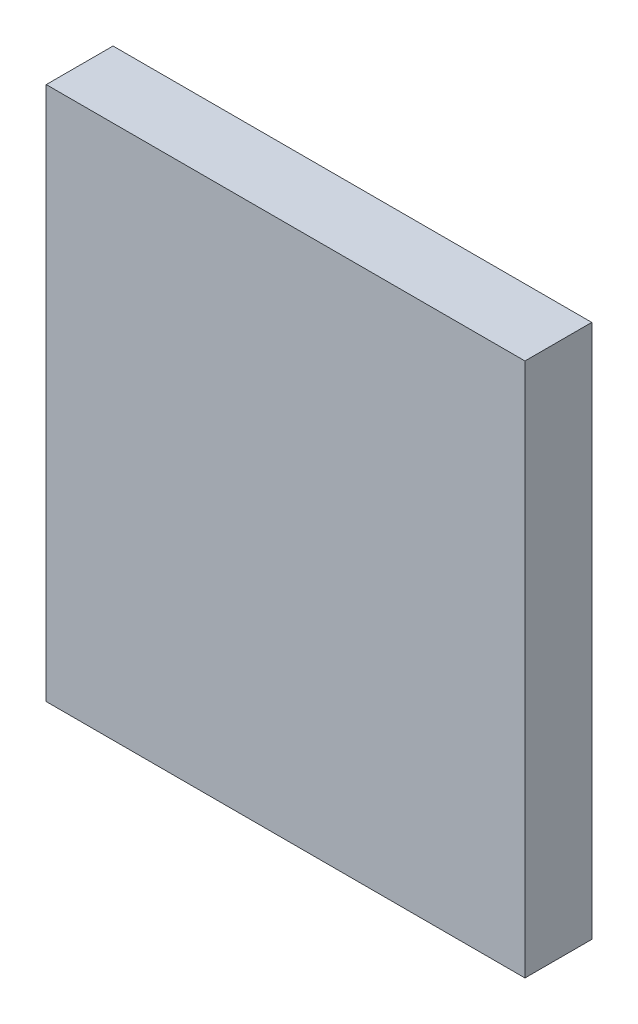
SolidWorks part; units mm, degrees
material "Клен"
ref_plane "Спереди" through (0, 0, 0) normal (0, 0, 1) x (1, 0, 0)
ref_plane "Сверху" through (0, 0, 0) normal (0, 1, 0) x (1, 0, 0)
ref_plane "Справа" through (0, 0, 0) normal (1, 0, 0) x (0, 0, -1)
sketch "Эскиз1" plane through (0, 0, 0) normal (0, 0, 1) x (1, 0, 0)
  line L1 (-21.5, 0) -> (21.5, 0)
  line L2 (-21.5, 0) -> (-21.5, 48)
  line L3 (-21.5, 48) -> (21.5, 48)
  line L4 (21.5, 0) -> (21.5, 48)
extrude "Бобышка-Вытянуть1" add sketch "Эскиз1" along normal blind 6
